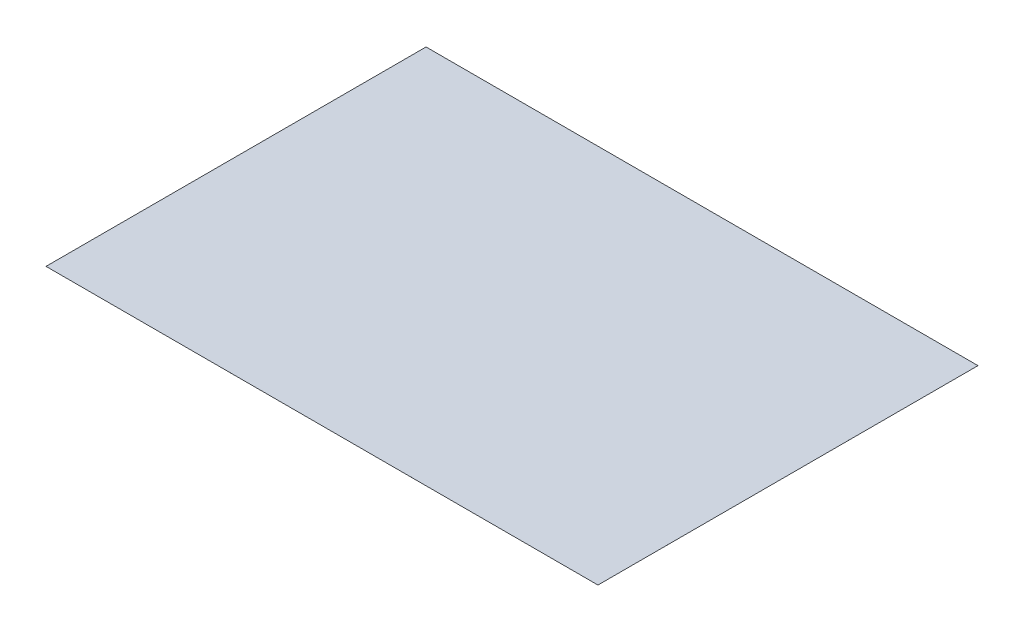
SolidWorks part; units mm, degrees
ref_plane "Front Plane" through (0, 0, 0) normal (0, 0, 1) x (1, 0, 0)
ref_plane "Top Plane" through (0, 0, 0) normal (0, 1, 0) x (1, 0, 0)
ref_plane "Right Plane" through (0, 0, 0) normal (1, 0, 0) x (0, 0, -1)
sketch "Sketch1" plane through (0, 0, 0) normal (0, 1, 0) x (1, 0, 0)
  line L1 (-33.9488, 19.2891) -> (23.2012, 19.2891)
  line L2 (-33.9488, 19.2891) -> (-33.9488, -20.0609)
  line L3 (-33.9488, -20.0609) -> (23.2012, -20.0609)
  line L4 (23.2012, 19.2891) -> (23.2012, -20.0609)
  dimension "D1" = 57.15
  dimension "D2" = 39.35
extrude "Boss-Extrude1" add sketch "Sketch1" along normal blind 0.0001
